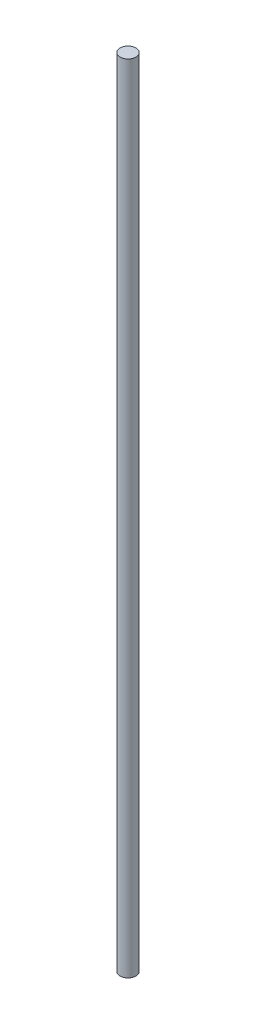
SolidWorks part; units mm, degrees
ref_plane "Спереди" through (0, 0, 0) normal (0, 0, 1) x (1, 0, 0)
ref_plane "Сверху" through (0, 0, 0) normal (0, 1, 0) x (1, 0, 0)
ref_plane "Справа" through (0, 0, 0) normal (1, 0, 0) x (0, 0, -1)
sketch "Эскиз1" plane through (0, 0, 0) normal (0, 1, 0) x (1, 0, 0)
  circle A0 centre (0, 0) radius 3
  dimension "D1" = 6
extrude "Бобышка-Вытянуть1" add sketch "Эскиз1" along normal blind 300.5
